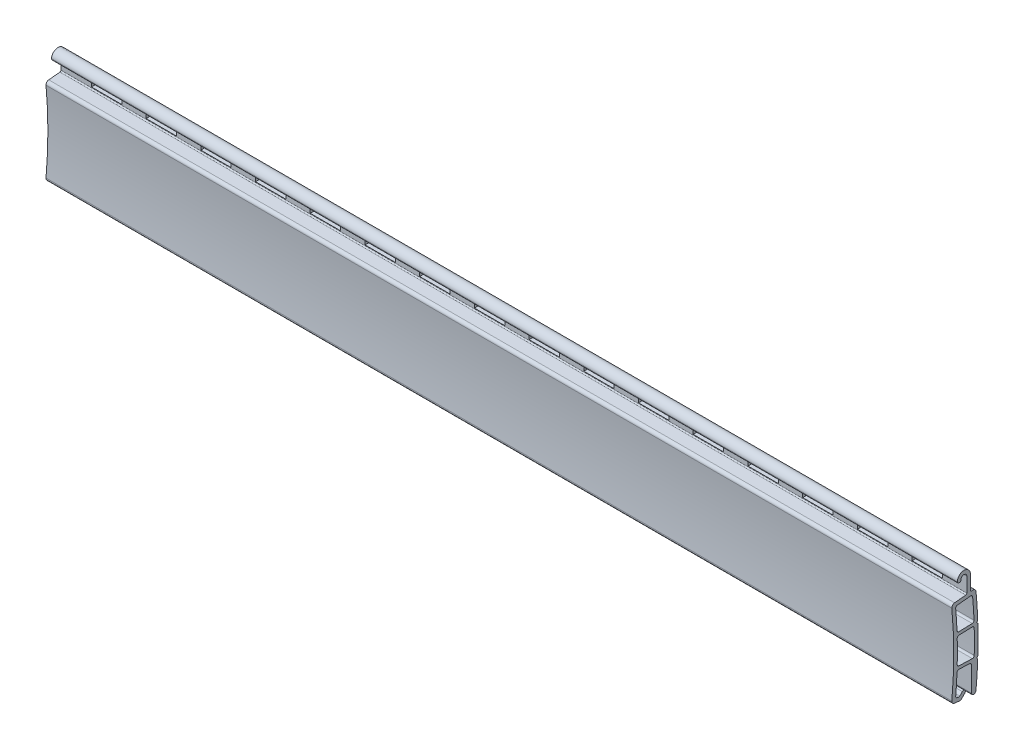
SolidWorks part; units mm, degrees
ref_plane "Plan de face" through (0, 0, 0) normal (0, 0, 1) x (1, 0, 0)
ref_plane "Plan de dessus" through (0, 0, 0) normal (0, 1, 0) x (1, 0, 0)
ref_plane "Plan de droite" through (0, 0, 0) normal (1, 0, 0) x (0, 0, -1)
sketch "Esquisse1" plane through (0, 0, 0) normal (1, 0, 0) x (0, 0, -1)
  line L0 (12.0644, 0) -> (-110.6603, 0) construction
  line L1 (21.1727, -7.5) -> (-42.9122, -7.5) construction
  line L2 (21.1727, 7.5) -> (-42.9122, 7.5) construction
  line L3 (0, -20.6998) -> (0, 49.585) construction
  line L4 (-75, -4.7823) -> (-75, 49.585) construction
  line L5 (-75, 0) -> (-0.3759, -7.5) construction
  line L6 (-75, 0) -> (4.0977, 2.6781) construction
  line L7 (-6.0875, 6.3229) -> (3.0361, 7.2399) construction
  line L8 (-1.0962, 16.7097) -> (-1.0962, -10.2001) construction
  line L9 (-75, 0) -> (-0.3759, 7.5) construction
  line L10 (-5.4319, 2.6056) -> (1.6637, 2.8458) construction
  line L11 (-5.4585, 2.1044) -> (1.8646, 2.3523) construction
  line L12 (-3.8601, 7.1498) -> (-2.0262, 7.3341)
  line L13 (-3.406, 6.5924) -> (-1.2169, 6.8125)
  line L14 (-3.1517, 2.6828) -> (-0.9529, 2.7572)
  line L15 (-3.1348, 2.1831) -> (-0.936, 2.2575)
  line L16 (-3.1348, -2.1831) -> (-0.936, -2.2575)
  line L17 (-3.1517, -2.6828) -> (-1.3861, -2.7426)
  line L18 (-3.406, -6.5924) -> (-3.1733, -6.6158)
  line L19 (-4.3559, -8.7961) -> (-4.3559, -4.9834) construction
  line L20 (-2.8559, -6.0442) -> (-2.8559, -8.7961) construction
  line L21 (-1.0962, -7.0843) -> (-1.0962, -3.0424)
  line L22 (-3.8601, -7.1498) -> (-2.9974, -7.2365)
  line L23 (-1.2462, 15.1007) -> (-1.2462, 5.976) construction
  line L24 (-3.3998, 15.1007) -> (-3.3998, 8.0529) construction
  line L25 (-1.8462, 15.9179) -> (-1.8462, 7.7124) construction
  line L26 (-2.7998, 15.1007) -> (-2.7998, 8.0529) construction
  line L27 (-3.5498, 14.9531) -> (-3.5498, -2.6693) construction
  line L28 (-6.339, 11) -> (4.0977, 11) construction
  line L29 (0.4492, 9.9232) -> (-4.6943, 9.9232) construction
  line L30 (-1.2462, 9.9232) -> (-1.2462, 7.6336)
  line L31 (-1.0262, 7.4346) -> (-0.8751, 7.4498)
  line L32 (-1.8462, 7.5331) -> (-1.8462, 9.9232)
  line L33 (-3.0998, 9.4222) -> (-3.0998, 10.1096) construction
  line L34 (-0.2428, 2.5311) -> (-0.05, 2.7375)
  line L35 (-0.2428, -2.5311) -> (-0.05, -2.7375)
  line L37 (-0.0365, 2.3383) -> (-0.2428, 2.5311)
  line L38 (-2.8559, -7.2508) -> (-1.6495, -6.0443) construction
  line L39 (-2.1654, -6.5603) -> (-3.1638, -5.5619) construction
  line L40 (-2.4074, -5.9537) -> (-3.3172, -6.8635) construction
  line L41 (-2.5897, -6.136) -> (-3.0119, -6.5583)
  line L42 (-2.0371, -6.0077) -> (-2.6593, -6.6299) construction
  line L43 (-2.1654, -6.5603) -> (-2.7553, -7.1502)
  line L45 (-0.0365, -2.3383) -> (-0.2428, -2.5311)
  arc A0 (-0.3388, -7.1203) -> (-0.05, -2.7375) centre (-75, 0) ccw
  arc A1 (-0.6633, 3.0694) -> (-0.888, 6.5403) centre (-75, 0) ccw
  arc A2 (-4.308, -6.6058) -> (-4.308, 6.6058) centre (-75, 0) ccw
  arc A3 (-3.4616, 2.9702) -> (-3.6749, 6.2677) centre (-75, 0) ccw
  arc A4 (-3.4616, -2.9702) -> (-3.1517, -2.6828) centre (-3.1619, -2.9826) cw
  arc A5 (-3.4616, -2.9702) -> (-3.6749, -6.2677) centre (-75, 0) cw
  arc A6 (-0.626, -1.9656) -> (-0.626, 1.9656) centre (-75, 0) ccw
  arc A7 (-3.4246, -1.8754) -> (-3.4246, 1.8754) centre (-75, 0) ccw
  arc A8 (-0.936, -2.2575) -> (-0.626, -1.9656) centre (-0.9259, -1.9577) ccw
  arc A9 (-3.1348, -2.1831) -> (-3.4246, -1.8754) centre (-3.1247, -1.8832) cw
  arc A10 (-3.1348, 2.1831) -> (-3.4246, 1.8754) centre (-3.1247, 1.8832) ccw
  arc A11 (-0.936, 2.2575) -> (-0.626, 1.9656) centre (-0.9259, 1.9577) cw
  arc A12 (-3.6749, 6.2677) -> (-3.406, 6.5924) centre (-3.376, 6.2939) cw
  arc A13 (-3.4616, 2.9702) -> (-3.1517, 2.6828) centre (-3.1619, 2.9826) ccw
  arc A14 (-0.6633, 3.0694) -> (-0.9529, 2.7572) centre (-0.9631, 3.057) cw
  arc A15 (-0.888, 6.5403) -> (-1.2169, 6.8125) centre (-1.1869, 6.514) ccw
  arc A16 (-1.0962, -7.0843) -> (-0.3388, -7.1203) centre (-0.7166, -7.0843) ccw
  arc A17 (-3.6749, -6.2677) -> (-3.406, -6.5924) centre (-3.376, -6.2939) ccw
  arc A18 (-1.3861, -2.7426) -> (-1.0962, -3.0424) centre (-1.3962, -3.0424) cw
  arc A19 (-1.2462, 9.9232) -> (-3.3998, 9.9232) centre (-2.323, 9.9232) ccw
  arc A20 (-1.8462, 9.9232) -> (-2.7998, 9.9232) centre (-2.323, 9.9232) ccw
  arc A21 (-3.3998, 9.9232) -> (-2.7998, 9.9232) centre (-3.0998, 9.9232) ccw
  arc A22 (-4.308, -6.6058) -> (-3.8601, -7.1498) centre (-3.8101, -6.6523) ccw
  arc A23 (-3.8601, 7.1498) -> (-4.308, 6.6058) centre (-3.8101, 6.6523) ccw
  arc A24 (-0.8751, 7.4498) -> (-0.3273, 6.999) centre (-0.8251, 6.9523) cw
  arc A25 (-1.8462, 7.5331) -> (-2.0262, 7.3341) centre (-2.0462, 7.5331) cw
  arc A26 (-1.0262, 7.4346) -> (-1.2462, 7.6336) centre (-1.0462, 7.6336) cw
  arc A27 (-3.1733, -6.6158) -> (-3.0119, -6.5583) centre (-3.1533, -6.4168) ccw
  arc A28 (-2.7553, -7.1502) -> (-2.9974, -7.2365) centre (-2.9674, -6.938) cw
  circle A29 centre (-75, 0) radius 74.8 construction
  arc A30 (-0.0365, -2.3383) -> (-0.0365, 2.3383) centre (-75, 0) ccw
  arc A31 (-0.05, 2.7375) -> (-0.3273, 6.999) centre (-75, 0) ccw
  arc A33 (-2.1654, -6.5603) -> (-2.5897, -6.136) centre (-2.3775, -6.3481) ccw
  point P38 (-0.6346, -2.2677)
  point P41 (-3.433, -2.173)
  point P44 (-3.433, 2.173)
  point P47 (-0.6346, 2.2677)
  point P50 (-3.7014, 6.5628)
  point P53 (-3.4499, 2.6727)
  point P56 (-0.6515, 2.7674)
  point P59 (-0.9153, 6.8428)
  point P85 (-1.0962, -2.7524)
  point P102 (-4.3559, -7.1)
  point P105 (-4.3559, 7.1)
  point P111 (-1.8462, 7.3522)
  point P114 (-1.2462, 7.4125)
  point P117 (-3.079, -6.6253)
  dimension "D4" = 3.8
  dimension "D5" = 0.5
  dimension "D9" = 0.6
  dimension "D11" = 0.15
  dimension "D12" = 0.3
  dimension "D20" = 0.6
  dimension "D21" = 0.3
  dimension "D22" = 0.9
  dimension "D23" = 0.3
  dimension "D3" = 0.15
  dimension "D8" = 0.3
  dimension "D15" = 0.5
  dimension "D16" = 0.2
  dimension "D17" = 0.2
  dimension "D24" = 45
  dimension "D1" = 15
  dimension "D2" = 7.5
  dimension "D6" = 0.25
  dimension "D7" = 0.6
  dimension "D10" = 0.6
  dimension "D13" = 3.5
  dimension "D14" = 0.3
  dimension "D18" = 45
  dimension "D19" = 1.5
extrude "Boss.-Extru.1" add sketch "Esquisse1" along normal blind 149
sketch "Esquisse2" plane through (0, 0, 1.2462) normal (0, 0, -1) x (-1, 0, 0)
  line L0 (-19, 8.6336) -> (-19, 7.6336)
  line L2 (-19, 8.6336) -> (-14, 8.6336)
  line L3 (-14, 8.6336) -> (-14, 7.6336)
  line L4 (-19, 7.6336) -> (-14, 7.6336)
  line L6 (-28, 8.6336) -> (-28, 7.6336)
  line L7 (-28, 8.6336) -> (-23, 8.6336)
  line L8 (-23, 8.6336) -> (-23, 7.6336)
  line L9 (-28, 7.6336) -> (-23, 7.6336)
  line L10 (-37, 8.6336) -> (-37, 7.6336)
  line L11 (-37, 8.6336) -> (-32, 8.6336)
  line L12 (-32, 8.6336) -> (-32, 7.6336)
  line L13 (-37, 7.6336) -> (-32, 7.6336)
  line L14 (-46, 8.6336) -> (-46, 7.6336)
  line L15 (-46, 8.6336) -> (-41, 8.6336)
  line L16 (-41, 8.6336) -> (-41, 7.6336)
  line L17 (-46, 7.6336) -> (-41, 7.6336)
  line L18 (-55, 8.6336) -> (-55, 7.6336)
  line L19 (-55, 8.6336) -> (-50, 8.6336)
  line L20 (-50, 8.6336) -> (-50, 7.6336)
  line L21 (-55, 7.6336) -> (-50, 7.6336)
  line L22 (-64, 8.6336) -> (-64, 7.6336)
  line L23 (-64, 8.6336) -> (-59, 8.6336)
  line L24 (-59, 8.6336) -> (-59, 7.6336)
  line L25 (-64, 7.6336) -> (-59, 7.6336)
  line L26 (-73, 8.6336) -> (-73, 7.6336)
  line L27 (-73, 8.6336) -> (-68, 8.6336)
  line L28 (-68, 8.6336) -> (-68, 7.6336)
  line L29 (-73, 7.6336) -> (-68, 7.6336)
  line L30 (-82, 8.6336) -> (-82, 7.6336)
  line L31 (-82, 8.6336) -> (-77, 8.6336)
  line L32 (-77, 8.6336) -> (-77, 7.6336)
  line L33 (-82, 7.6336) -> (-77, 7.6336)
  line L34 (-91, 8.6336) -> (-91, 7.6336)
  line L35 (-91, 8.6336) -> (-86, 8.6336)
  line L36 (-86, 8.6336) -> (-86, 7.6336)
  line L37 (-91, 7.6336) -> (-86, 7.6336)
  line L38 (-100, 8.6336) -> (-100, 7.6336)
  line L39 (-100, 8.6336) -> (-95, 8.6336)
  line L40 (-95, 8.6336) -> (-95, 7.6336)
  line L41 (-100, 7.6336) -> (-95, 7.6336)
  line L42 (-109, 8.6336) -> (-109, 7.6336)
  line L43 (-109, 8.6336) -> (-104, 8.6336)
  line L44 (-104, 8.6336) -> (-104, 7.6336)
  line L45 (-109, 7.6336) -> (-104, 7.6336)
  line L46 (-118, 8.6336) -> (-118, 7.6336)
  line L47 (-118, 8.6336) -> (-113, 8.6336)
  line L48 (-113, 8.6336) -> (-113, 7.6336)
  line L49 (-118, 7.6336) -> (-113, 7.6336)
  line L50 (-127, 8.6336) -> (-127, 7.6336)
  line L51 (-127, 8.6336) -> (-122, 8.6336)
  line L52 (-122, 8.6336) -> (-122, 7.6336)
  line L53 (-127, 7.6336) -> (-122, 7.6336)
  line L54 (-136, 8.6336) -> (-136, 7.6336)
  line L55 (-136, 8.6336) -> (-131, 8.6336)
  line L56 (-131, 8.6336) -> (-131, 7.6336)
  line L57 (-136, 7.6336) -> (-131, 7.6336)
  line L58 (-145, 8.6336) -> (-145, 7.6336)
  line L59 (-145, 8.6336) -> (-140, 8.6336)
  line L60 (-140, 8.6336) -> (-140, 7.6336)
  line L61 (-145, 7.6336) -> (-140, 7.6336)
  line L79 (-10, 8.6336) -> (-10, 7.6336)
  line L80 (-10, 8.6336) -> (-5, 8.6336)
  line L81 (-5, 8.6336) -> (-5, 7.6336)
  line L82 (-10, 7.6336) -> (-5, 7.6336)
extrude "Enlèv. mat.-Extru.1" cut sketch "Esquisse2" against normal blind 10
ref_plane "Plan1" through (74.5, 0, 0) normal (1, 0, 0) x (0, 0, -1)
ref_plane "Plan2" through (3, 0, 0) normal (1, 0, 0) x (0, 0, -1)
sketch "Esquisse3" plane through (3, 0, 0) normal (1, 0, 0) x (0, 0, -1)
  line L0 (-0.7314, 7.0271) -> (-3.9501, 6.7815)
  line L1 (-3.9501, 6.7815) -> (-3.6447, 2.4302)
  line L2 (-3.6447, 2.4302) -> (-3.6447, -2.4067)
  line L3 (-3.6447, -2.4067) -> (-0.3694, -2.5229)
  line L4 (-0.3694, -2.5229) -> (-0.3912, 2.5693)
  line L5 (-0.3912, 2.5693) -> (-0.7314, 7.0271)
extrude "Boss.-Extru.2" add sketch "Esquisse3" along normal blind 0.8
mirror "Symétrie1" about plane through (74.5, 0, 0) normal (1, 0, 0) of "Boss.-Extru.2"
